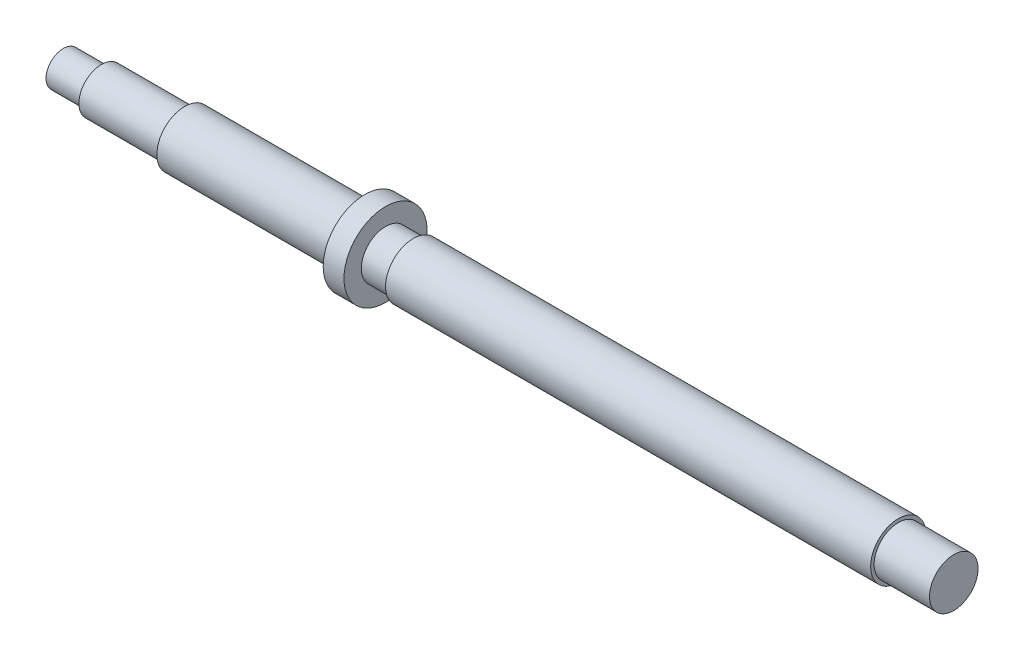
SolidWorks part; units mm, degrees
ref_plane "Front Plane" through (0, 0, 0) normal (0, 0, 1) x (1, 0, 0)
ref_plane "Top Plane" through (0, 0, 0) normal (0, 1, 0) x (1, 0, 0)
ref_plane "Right Plane" through (0, 0, 0) normal (1, 0, 0) x (0, 0, -1)
sketch "Sketch1" plane through (0, 0, 0) normal (0, 1, 0) x (1, 0, 0)
  line L0 (0, 0) -> (11, 0)
  line L1 (11, 0) -> (11, -1.5)
  line L2 (11, -1.5) -> (35, -1.5)
  line L3 (35, -1.5) -> (35, -3)
  line L4 (35, -3) -> (87, -3)
  line L5 (87, -3) -> (87, -7)
  line L6 (87, -7) -> (93, -7)
  line L7 (93, -7) -> (93, -2)
  line L8 (0, 5) -> (54.3344, 5) construction
  line L9 (93, -2) -> (101, -2)
  line L10 (101, -2) -> (101, -3)
  line L11 (101, -3) -> (241, -3)
  line L12 (241, -3) -> (241, -2)
  line L13 (241, -2) -> (257, -2)
  line L14 (257, -2) -> (257, 5)
  line L15 (0, 0) -> (0, 5)
  line L16 (0, 5) -> (257, 5)
  dimension "D1" = 5
  dimension "D2" = 8
  dimension "D3" = 6.5
  dimension "D4" = 11
  dimension "D5" = 24
  dimension "D6" = 52
  dimension "D7" = 6
  dimension "D8" = 12
  dimension "D9" = 7
  dimension "D10" = 8
  dimension "D11" = 140
  dimension "D12" = 8
  dimension "D13" = 7
  dimension "D14" = 16
revolve "Revolve1" add sketch "Sketch1" angle 360 about L8
